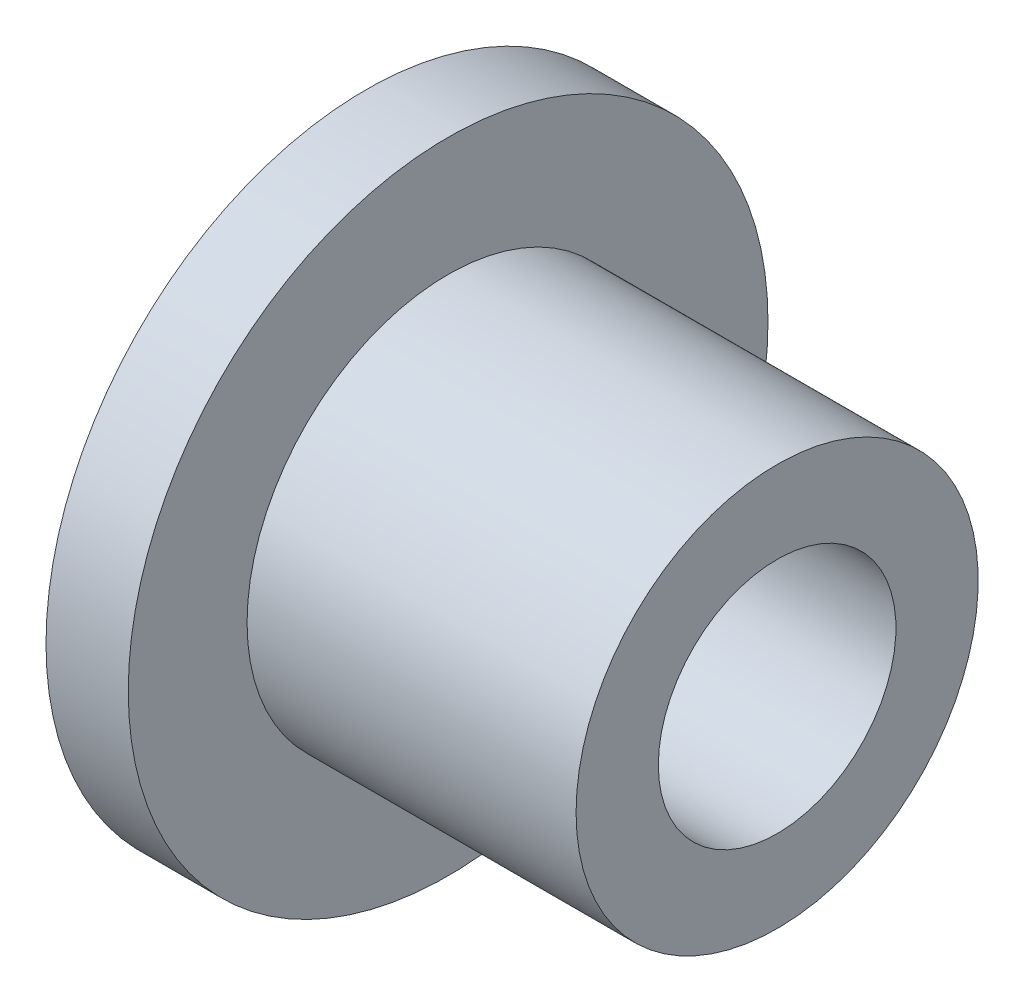
SolidWorks part; units mm, degrees
ref_plane "Front Plane" through (0, 0, 0) normal (0, 0, 1) x (1, 0, 0)
ref_plane "Top Plane" through (0, 0, 0) normal (0, 1, 0) x (1, 0, 0)
ref_plane "Right Plane" through (0, 0, 0) normal (1, 0, 0) x (0, 0, -1)
sketch "Sketch1" plane through (0, 0, 0) normal (0, 0, 1) x (1, 0, 0)
  line L0 (0, 0) -> (163.6701, 0) construction
  line L1 (-1.8093, 52.5) -> (-1.8093, 15)
  line L2 (-1.8093, 52.5) -> (11.6907, 52.5)
  line L3 (11.6907, 52.5) -> (11.6907, 33)
  line L4 (11.6907, 33) -> (65.6907, 33)
  line L5 (65.6907, 33) -> (65.6907, 19.5)
  line L6 (65.6907, 19.5) -> (11.6907, 19.5)
  line L7 (11.6907, 19.5) -> (11.6907, 15)
  line L8 (11.6907, 15) -> (-1.8093, 15)
  point P3 (0, 0)
  point P12 (0, 0)
  point P13 (0, 0)
  point P14 (0, 0)
  dimension "D1" = 54
  dimension "D2" = 19.5
  dimension "D3" = 33
  dimension "D4" = 52.5
  dimension "D5" = 15
  dimension "D6" = 13.5
revolve "Revolve1" add sketch "Sketch1" angle 360 about L0
